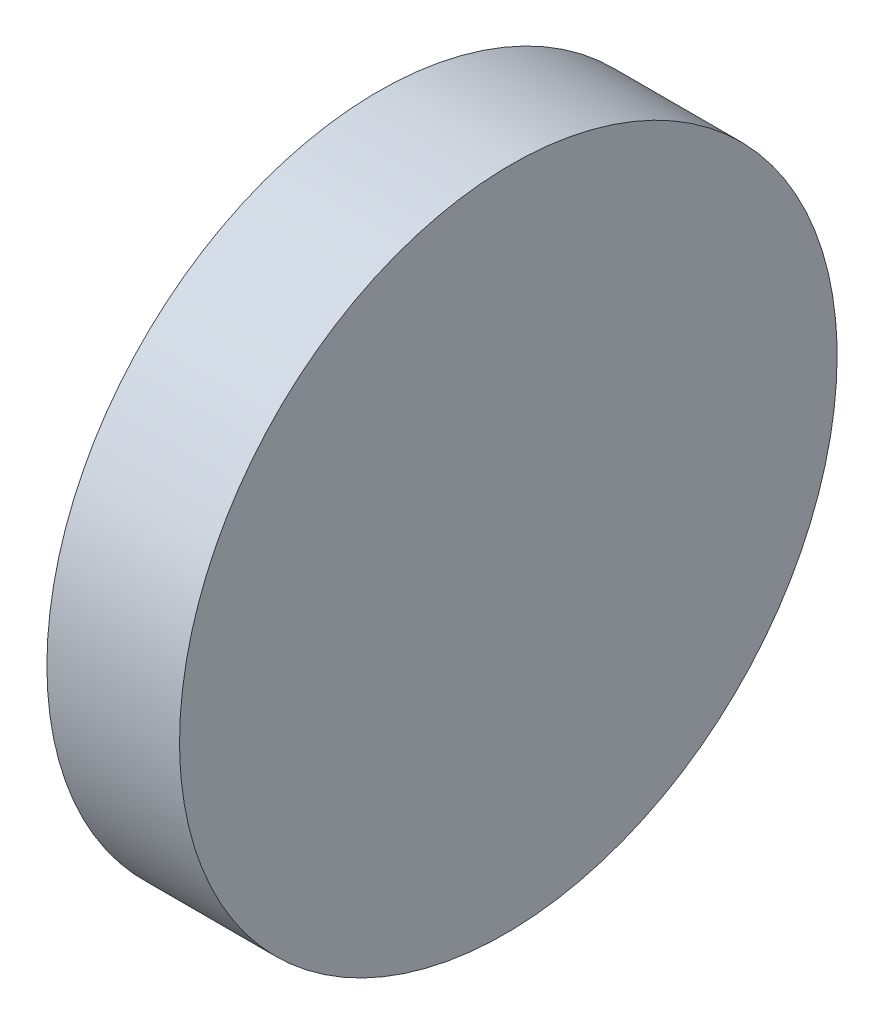
SolidWorks part; units mm, degrees
ref_plane "前视基准面" through (0, 0, 0) normal (0, 0, 1) x (1, 0, 0)
ref_plane "上视基准面" through (0, 0, 0) normal (0, 1, 0) x (1, 0, 0)
ref_plane "右视基准面" through (0, 0, 0) normal (1, 0, 0) x (0, 0, -1)
sketch "草图1" plane through (0, 0, 0) normal (0, 1, 0) x (1, 0, 0)
  line L0 (-12.1202, 0) -> (19.0875, 0) construction
  line L1 (0, 12.5) -> (0, -12.5)
  line L2 (0, -12.5) -> (5, -12.5)
  line L3 (5, -12.5) -> (4.7818, 12.5)
  line L4 (0, 12.5) -> (4.7818, 12.5)
  point P5 (0, 0)
  dimension "D1" = 5
  dimension "D2" = 25
  dimension "D3" = 0.5
extrude "凸台-拉伸1" add sketch "草图1" along normal blind 25
sketch "草图5" plane through (0, 0, 0) normal (-1, 0, 0) x (0, 0, 1)
  line L0 (0, 0) -> (0, 25) construction
  line L1 (-12.5, 25) -> (12.5, 25) construction
  line L2 (0, 25) -> (0.9302, 12.292) construction
  line L3 (-12.5, 12.5) -> (12.5, 12.5) construction
  line L4 (-12.5, 25) -> (-12.5, 0) construction
  line L5 (12.5, 25) -> (12.5, 0) construction
  line L6 (12.5, 12.5) -> (6.6453, 6.1075) construction
  line L11 (-12.5, 0) -> (12.5, 0)
  line L12 (12.5, 0) -> (12.5, 25)
  line L13 (12.5, 25) -> (-12.5, 25)
  line L14 (-12.5, 25) -> (-12.5, 0)
  line L15 (-12.5, 0) -> (12.5, 0)
  line L16 (12.5, 0) -> (12.5, 25)
  line L17 (12.5, 25) -> (-12.5, 25)
  line L18 (-12.5, 25) -> (-12.5, 0)
  circle A0 centre (0, 12.5) radius 12.5
  line M5 (-12.5, 0) -> (12.5, 0)
  line M6 (12.5, 0) -> (12.5, 25)
  line M7 (12.5, 25) -> (-12.5, 25)
  line M8 (-12.5, 25) -> (-12.5, 0)
  dimension "D1" = 25
  dimension "D2" = 0
extrude "切除-拉伸2" cut sketch "草图5" against normal blind 12.5 contours A0 L17 M8 | A0 L18 M5 | A0 L15 M6 | A0 L16 M7
